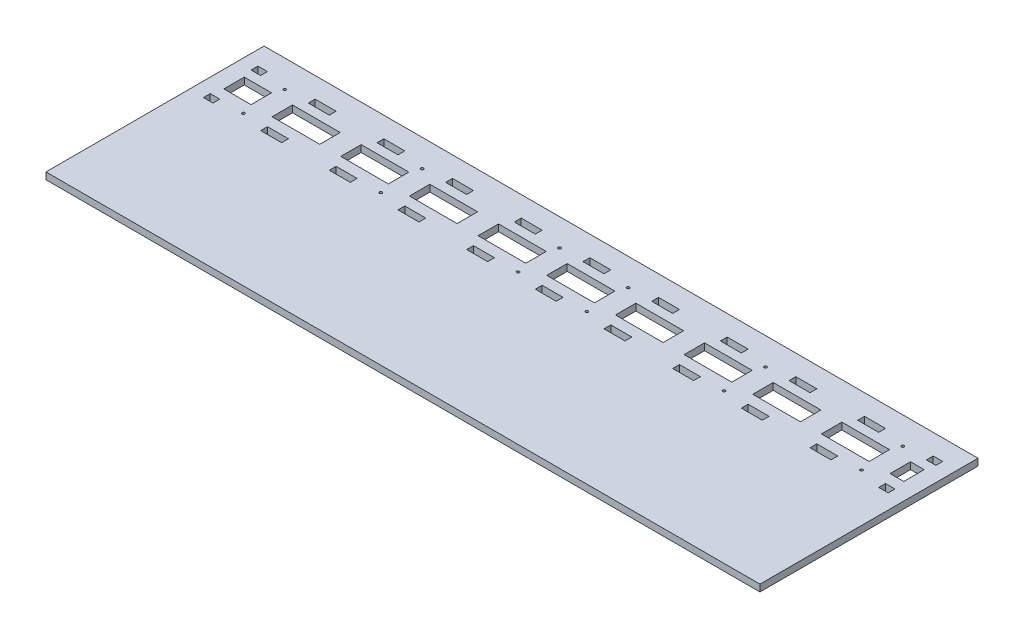
SolidWorks part; units mm, degrees
material "Pine"
ref_plane "Front Plane" through (0, 0, 0) normal (0, 0, 1) x (1, 0, 0)
ref_plane "Top Plane" through (0, 0, 0) normal (0, 1, 0) x (1, 0, 0)
ref_plane "Right Plane" through (0, 0, 0) normal (1, 0, 0) x (0, 0, -1)
sketch "Sketch1" plane through (0, 0, 0) normal (0, 1, 0) x (1, 0, 0)
  line L1 (0, 0) -> (1330.706, 0)
  line L2 (0, 0) -> (0, 406.4)
  line L3 (0, 406.4) -> (1330.706, 406.4)
  line L4 (1330.706, 0) -> (1330.706, 406.4)
  dimension "D1" = 1330.706
  dimension "D2" = 406.4
extrude "Boss-Extrude1" add sketch "Sketch1" along normal blind 12.7
sketch "Sketch3" plane through (0, 0, 0) normal (0, -1, 0) x (1, 0, 0)
  line L1 (82.55, -337.82) -> (31.75, -337.82)
  line L2 (82.55, -337.82) -> (82.55, -299.72)
  line L3 (82.55, -299.72) -> (31.75, -299.72)
  line L4 (31.75, -337.82) -> (31.75, -299.72)
  line L5 (1330.706, -406.4) -> (0, -406.4) construction
  line L6 (0, -406.4) -> (0, 0) construction
  line L7 (249.6312, -299.72) -> (338.5312, -299.72)
  line L8 (121.6406, -299.72) -> (210.5406, -299.72)
  line L9 (121.6406, -299.72) -> (121.6406, -337.82)
  line L10 (121.6406, -337.82) -> (210.5406, -337.82)
  line L11 (210.5406, -299.72) -> (210.5406, -337.82)
  line L12 (249.6312, -299.72) -> (249.6312, -337.82)
  line L13 (249.6312, -337.82) -> (338.5312, -337.82)
  line L14 (338.5312, -299.72) -> (338.5312, -337.82)
  line L15 (26.67, -355.6) -> (44.45, -355.6)
  line L16 (377.6218, -299.72) -> (466.5218, -299.72)
  line L17 (377.6218, -299.72) -> (377.6218, -337.82)
  line L18 (377.6218, -337.82) -> (466.5218, -337.82)
  line L19 (466.5218, -299.72) -> (466.5218, -337.82)
  line L20 (0, -381) -> (1330.706, -381) construction
  line L21 (505.6124, -299.72) -> (594.5124, -299.72)
  line L22 (505.6124, -299.72) -> (505.6124, -337.82)
  line L23 (505.6124, -337.82) -> (594.5124, -337.82)
  line L24 (594.5124, -299.72) -> (594.5124, -337.82)
  line L25 (633.603, -299.72) -> (722.503, -299.72)
  line L26 (633.603, -299.72) -> (633.603, -337.82)
  line L27 (633.603, -337.82) -> (722.503, -337.82)
  line L28 (722.503, -299.72) -> (722.503, -337.82)
  line L29 (761.5936, -299.72) -> (850.4936, -299.72)
  line L30 (761.5936, -299.72) -> (761.5936, -337.82)
  line L31 (761.5936, -337.82) -> (850.4936, -337.82)
  line L32 (850.4936, -299.72) -> (850.4936, -337.82)
  line L33 (889.5842, -299.72) -> (978.4842, -299.72)
  line L34 (889.5842, -299.72) -> (889.5842, -337.82)
  line L35 (889.5842, -337.82) -> (978.4842, -337.82)
  line L36 (978.4842, -299.72) -> (978.4842, -337.82)
  line L37 (1017.5748, -299.72) -> (1106.4748, -299.72)
  line L38 (1017.5748, -299.72) -> (1017.5748, -337.82)
  line L39 (1017.5748, -337.82) -> (1106.4748, -337.82)
  line L40 (1106.4748, -299.72) -> (1106.4748, -337.82)
  line L41 (1145.5654, -299.72) -> (1234.4654, -299.72)
  line L42 (1145.5654, -299.72) -> (1145.5654, -337.82)
  line L43 (1145.5654, -337.82) -> (1234.4654, -337.82)
  line L44 (1234.4654, -299.72) -> (1234.4654, -337.82)
  line L45 (1273.556, -299.72) -> (1298.956, -299.72)
  line L46 (1273.556, -299.72) -> (1273.556, -337.82)
  line L47 (1273.556, -337.82) -> (1298.956, -337.82)
  line L48 (1298.956, -299.72) -> (1298.956, -337.82)
  line L49 (1330.706, 0) -> (1330.706, -406.4) construction
  line L50 (26.67, -355.6) -> (26.67, -368.3)
  line L51 (26.67, -368.3) -> (44.45, -368.3)
  line L52 (44.45, -355.6) -> (44.45, -368.3)
  line L53 (389.3312, -266.7) -> (428.4218, -266.7)
  line L54 (26.67, -266.7) -> (44.45, -266.7)
  line L55 (26.67, -266.7) -> (26.67, -279.4)
  line L56 (26.67, -279.4) -> (44.45, -279.4)
  line L57 (44.45, -266.7) -> (44.45, -279.4)
  line L58 (133.35, -266.7) -> (172.4406, -266.7)
  line L59 (133.35, -266.7) -> (133.35, -279.4)
  line L60 (133.35, -279.4) -> (172.4406, -279.4)
  line L61 (172.4406, -266.7) -> (172.4406, -279.4)
  line L62 (133.35, -355.6) -> (172.4406, -355.6)
  line L63 (133.35, -355.6) -> (133.35, -368.3)
  line L64 (133.35, -368.3) -> (172.4406, -368.3)
  line L65 (172.4406, -355.6) -> (172.4406, -368.3)
  line L66 (389.3312, -266.7) -> (389.3312, -279.4)
  line L67 (261.3406, -266.7) -> (300.4312, -266.7)
  line L68 (261.3406, -266.7) -> (261.3406, -279.4)
  line L69 (261.3406, -279.4) -> (300.4312, -279.4)
  line L70 (300.4312, -266.7) -> (300.4312, -279.4)
  line L71 (261.3406, -355.6) -> (300.4312, -355.6)
  line L72 (261.3406, -355.6) -> (261.3406, -368.3)
  line L73 (261.3406, -368.3) -> (300.4312, -368.3)
  line L74 (300.4312, -355.6) -> (300.4312, -368.3)
  line L75 (389.3312, -279.4) -> (428.4218, -279.4)
  line L76 (428.4218, -266.7) -> (428.4218, -279.4)
  line L77 (389.3312, -355.6) -> (428.4218, -355.6)
  line L78 (389.3312, -355.6) -> (389.3312, -368.3)
  line L79 (389.3312, -368.3) -> (428.4218, -368.3)
  line L80 (428.4218, -355.6) -> (428.4218, -368.3)
  line L81 (517.3218, -355.6) -> (556.4124, -355.6)
  line L82 (517.3218, -355.6) -> (517.3218, -368.3)
  line L83 (517.3218, -368.3) -> (556.4124, -368.3)
  line L84 (556.4124, -355.6) -> (556.4124, -368.3)
  line L85 (517.3218, -266.7) -> (556.4124, -266.7)
  line L86 (517.3218, -266.7) -> (517.3218, -279.4)
  line L87 (517.3218, -279.4) -> (556.4124, -279.4)
  line L88 (556.4124, -266.7) -> (556.4124, -279.4)
  line L89 (645.3124, -355.6) -> (684.403, -355.6)
  line L90 (645.3124, -355.6) -> (645.3124, -368.3)
  line L91 (645.3124, -368.3) -> (684.403, -368.3)
  line L92 (684.403, -355.6) -> (684.403, -368.3)
  line L93 (645.3124, -266.7) -> (684.403, -266.7)
  line L94 (645.3124, -266.7) -> (645.3124, -279.4)
  line L95 (645.3124, -279.4) -> (684.403, -279.4)
  line L96 (684.403, -266.7) -> (684.403, -279.4)
  line L97 (773.303, -266.7) -> (812.3936, -266.7)
  line L98 (773.303, -266.7) -> (773.303, -279.4)
  line L99 (773.303, -279.4) -> (812.3936, -279.4)
  line L100 (812.3936, -266.7) -> (812.3936, -279.4)
  line L101 (901.2936, -355.6) -> (940.3842, -355.6)
  line L102 (773.303, -355.6) -> (812.3936, -355.6)
  line L103 (773.303, -355.6) -> (773.303, -368.3)
  line L104 (773.303, -368.3) -> (812.3936, -368.3)
  line L105 (812.3936, -355.6) -> (812.3936, -368.3)
  line L106 (901.2936, -266.7) -> (940.3842, -266.7)
  line L107 (901.2936, -266.7) -> (901.2936, -279.4)
  line L108 (901.2936, -279.4) -> (940.3842, -279.4)
  line L109 (940.3842, -266.7) -> (940.3842, -279.4)
  line L110 (901.2936, -355.6) -> (901.2936, -368.3)
  line L111 (901.2936, -368.3) -> (940.3842, -368.3)
  line L112 (940.3842, -355.6) -> (940.3842, -368.3)
  line L113 (1029.2842, -355.6) -> (1068.3748, -355.6)
  line L114 (1029.2842, -266.7) -> (1068.3748, -266.7)
  line L115 (1029.2842, -266.7) -> (1029.2842, -279.4)
  line L116 (1029.2842, -279.4) -> (1068.3748, -279.4)
  line L117 (1068.3748, -266.7) -> (1068.3748, -279.4)
  line L118 (1029.2842, -355.6) -> (1029.2842, -368.3)
  line L119 (1029.2842, -368.3) -> (1068.3748, -368.3)
  line L120 (1068.3748, -355.6) -> (1068.3748, -368.3)
  line L122 (1157.2748, -266.7) -> (1196.3654, -266.7)
  line L123 (1157.2748, -266.7) -> (1157.2748, -279.4)
  line L124 (1157.2748, -279.4) -> (1196.3654, -279.4)
  line L125 (1196.3654, -266.7) -> (1196.3654, -279.4)
  line L126 (1157.2748, -355.6) -> (1196.3654, -355.6)
  line L127 (1157.2748, -355.6) -> (1157.2748, -368.3)
  line L128 (1157.2748, -368.3) -> (1196.3654, -368.3)
  line L129 (1196.3654, -355.6) -> (1196.3654, -368.3)
  line L130 (1285.2654, -355.6) -> (1303.0454, -355.6)
  line L131 (1285.2654, -355.6) -> (1285.2654, -368.3)
  line L132 (1285.2654, -368.3) -> (1303.0454, -368.3)
  line L133 (1303.0454, -355.6) -> (1303.0454, -368.3)
  line L135 (1285.2654, -266.7) -> (1303.0454, -266.7)
  line L136 (1285.2654, -266.7) -> (1285.2654, -279.4)
  line L137 (1285.2654, -279.4) -> (1303.0454, -279.4)
  line L138 (1303.0454, -266.7) -> (1303.0454, -279.4)
  circle A0 centre (89.3953, -278.5618) radius 2.54
  circle A1 centre (89.3953, -355.6) radius 2.54
  circle A2 centre (345.3765, -278.5618) radius 2.54
  circle A3 centre (345.3765, -355.6) radius 2.54
  circle A4 centre (601.3577, -278.5618) radius 2.54
  circle A5 centre (601.3577, -355.6) radius 2.54
  circle A6 centre (729.3483, -278.5618) radius 2.54
  circle A7 centre (729.3483, -355.6) radius 2.54
  circle A8 centre (985.3295, -278.5618) radius 2.54
  circle A9 centre (985.3295, -355.6) radius 2.54
  circle A10 centre (1241.3107, -278.5618) radius 2.54
  circle A11 centre (1241.3107, -355.6) radius 2.54
  dimension "D47" = 5.08
  dimension "D48" = 5.08
  dimension "D49" = 5.08
  dimension "D50" = 5.08
  dimension "D51" = 5.08
  dimension "D52" = 5.08
  dimension "D53" = 5.08
  dimension "D54" = 5.08
  dimension "D55" = 5.08
  dimension "D56" = 5.08
  dimension "D57" = 5.08
  dimension "D58" = 5.08
  dimension "D116" = 12.7
  dimension "D1" = 50.8
  dimension "D2" = 38.1
  dimension "D4" = 31.75
  dimension "D5" = 38.1
  dimension "D6" = 88.9
  dimension "D7" = 39.0906
  dimension "D8" = 43.18
  dimension "D9" = 88.9
  dimension "D10" = 39.0906
  dimension "D11" = 38.1
  dimension "D12" = 88.9
  dimension "D13" = 38.1
  dimension "D14" = 39.0906
  dimension "D15" = 43.18
  dimension "D16" = 43.18
  dimension "D17" = 88.9
  dimension "D18" = 88.9
  dimension "D19" = 88.9
  dimension "D20" = 39.0906
  dimension "D21" = 38.1
  dimension "D22" = 38.1
  dimension "D23" = 38.1
  dimension "D24" = 43.18
  dimension "D25" = 43.18
  dimension "D26" = 43.18
  dimension "D27" = 39.0906
  dimension "D28" = 39.0906
  dimension "D29" = 88.9
  dimension "D30" = 88.9
  dimension "D31" = 88.9
  dimension "D32" = 39.0906
  dimension "D33" = 38.1
  dimension "D34" = 38.1
  dimension "D35" = 39.0906
  dimension "D36" = 43.18
  dimension "D37" = 43.18
  dimension "D38" = 43.18
  dimension "D39" = 39.0906
  dimension "D40" = 38.1
  dimension "D41" = 39.0906
  dimension "D42" = 38.1
  dimension "D43" = 25.4
  dimension "D44" = 43.18
  dimension "D45" = 25.4
  dimension "D46" = 43.18
  dimension "D59" = 17.78
  dimension "D60" = 12.7
  dimension "D61" = 12.7
  dimension "D62" = 26.67
  dimension "D63" = 26.67
  dimension "D64" = 76.2
  dimension "D65" = 12.7
  dimension "D66" = 17.78
  dimension "D67" = 12.7
  dimension "D68" = 39.0906
  dimension "D69" = 88.9
  dimension "D70" = 88.9
  dimension "D71" = 12.7
  dimension "D72" = 39.0906
  dimension "D73" = 12.7
  dimension "D74" = 76.2
  dimension "D75" = 39.0906
  dimension "D76" = 12.7
  dimension "D77" = 88.9
  dimension "D78" = 12.7
  dimension "D79" = 39.0906
  dimension "D80" = 12.7
  dimension "D81" = 76.2
  dimension "D82" = 88.9
  dimension "D83" = 12.7
  dimension "D84" = 39.0906
  dimension "D85" = 39.0906
  dimension "D86" = 12.7
  dimension "D87" = 12.7
  dimension "D88" = 88.9
  dimension "D89" = 76.2
  dimension "D90" = 88.9
  dimension "D91" = 12.7
  dimension "D92" = 39.0906
  dimension "D93" = 12.7
  dimension "D94" = 39.0906
  dimension "D95" = 12.7
  dimension "D96" = 76.2
  dimension "D97" = 88.9
  dimension "D98" = 88.9
  dimension "D99" = 12.7
  dimension "D100" = 39.0906
  dimension "D101" = 12.7
  dimension "D102" = 88.9
  dimension "D103" = 76.2
  dimension "D104" = 88.9
  dimension "D105" = 12.7
  dimension "D106" = 39.0906
  dimension "D107" = 12.7
  dimension "D108" = 39.0906
  dimension "D109" = 12.7
  dimension "D110" = 88.9
  dimension "D111" = 88.9
  dimension "D112" = 76.2
  dimension "D113" = 12.7
  dimension "D114" = 39.0906
  dimension "D115" = 12.7
  dimension "D117" = 39.0906
  dimension "D118" = 39.0906
  dimension "D119" = 88.9
  dimension "D120" = 88.9
  dimension "D121" = 12.7
  dimension "D122" = 76.2
  dimension "D123" = 12.7
  dimension "D124" = 88.9
  dimension "D125" = 39.0906
  dimension "D126" = 12.7
  dimension "D127" = 88.9
  dimension "D128" = 76.2
  dimension "D129" = 39.0906
  dimension "D130" = 12.7
  dimension "D131" = 88.9
  dimension "D132" = 39.0906
  dimension "D133" = 12.7
  dimension "D134" = 76.2
  dimension "D135" = 12.7
  dimension "D136" = 12.7
  dimension "D137" = 88.9
  dimension "D138" = 39.0906
  dimension "D139" = 88.9
  dimension "D140" = 17.78
  dimension "D141" = 17.78
  dimension "D142" = 12.7
  dimension "D143" = 12.7
  dimension "D144" = 76.2
  dimension "D145" = 88.9
  dimension "D146" = 12.7
extrude "Cut-Extrude2" cut sketch "Sketch3" against normal through all
